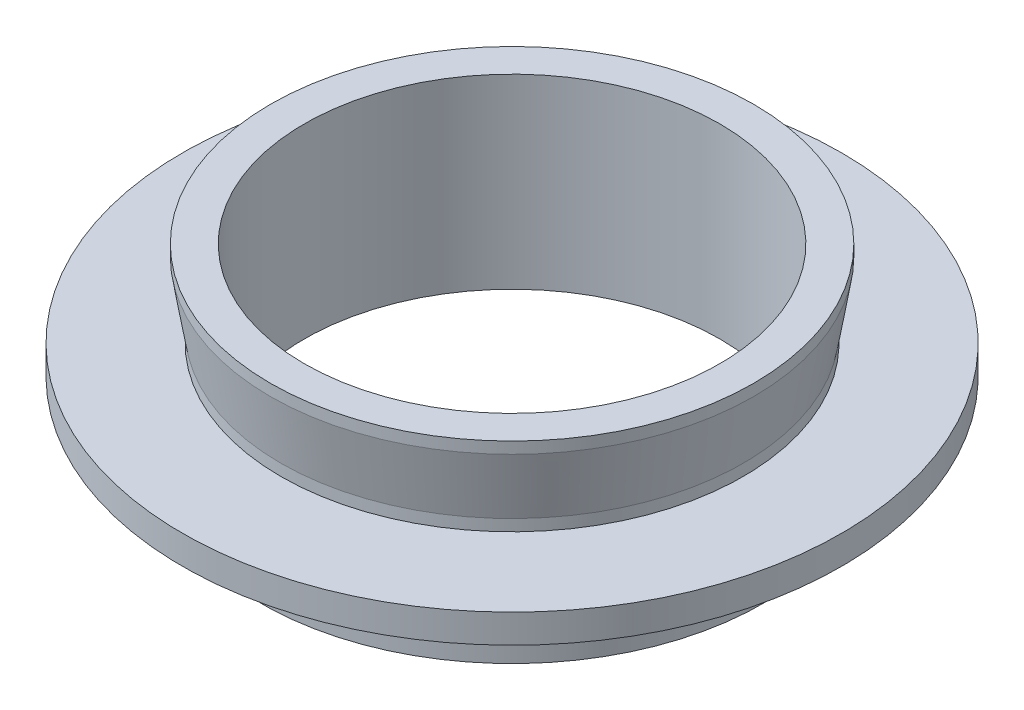
SolidWorks part; units mm, degrees
ref_plane "前视基准面" through (0, 0, 0) normal (0, 0, 1) x (1, 0, 0)
ref_plane "上视基准面" through (0, 0, 0) normal (0, 1, 0) x (1, 0, 0)
ref_plane "右视基准面" through (0, 0, 0) normal (1, 0, 0) x (0, 0, -1)
sketch "草图1" plane through (0, 0, 0) normal (0, 0, 1) x (1, 0, 0)
  line L0 (0, 0) -> (0, 73.2965) construction
  line L1 (-14.5, 0) -> (-14.5, 13)
  line L2 (-14.5, 13) -> (-16.865, 13)
  line L3 (-16.865, 13) -> (-16.865, 12.2)
  line L4 (-16.865, 12.2) -> (-16.135, 7.8)
  line L5 (-16.135, 7.8) -> (-16.135, 7)
  line L6 (-16.135, 7) -> (-23, 7)
  line L7 (-23, 7) -> (-23, 5)
  line L8 (-23, 5) -> (-17.1, 5)
  line L9 (-17.1, 5) -> (-17.1, 4)
  line L10 (-17.1, 4) -> (-17.5, 4)
  line L11 (-17.5, 4) -> (-17.5, 0)
  line L12 (-17.5, 0) -> (-14.5, 0)
  dimension "D1" = 14.5
  dimension "D2" = 16.865
  dimension "D3" = 16.135
  dimension "D4" = 17.5
  dimension "D5" = 17.1
  dimension "D6" = 13
  dimension "D7" = 6
  dimension "D8" = 2
  dimension "D9" = 1
  dimension "D10" = 0.8
  dimension "D11" = 0.8
  dimension "D12" = 0
  dimension "D13" = 23
revolve "旋转1" add sketch "草图1" angle 360 about L0
cosmetic thread "装饰螺纹线1"
cosmetic thread "装饰螺纹线2"
